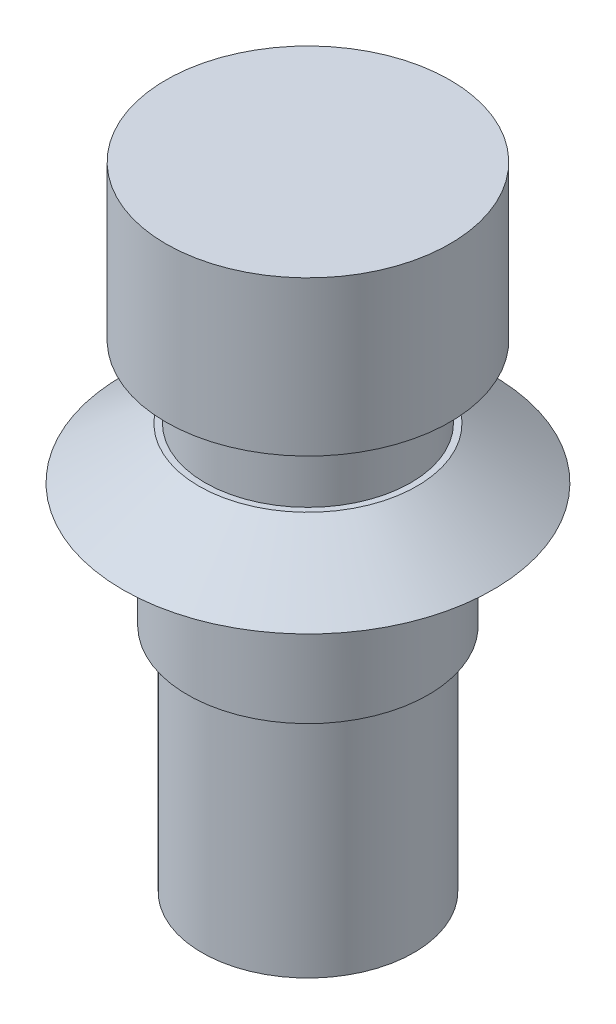
SolidWorks part; units mm, degrees
ref_plane "Спереди" through (0, 0, 0) normal (0, 0, 1) x (1, 0, 0)
ref_plane "Сверху" through (0, 0, 0) normal (0, 1, 0) x (1, 0, 0)
ref_plane "Справа" through (0, 0, 0) normal (1, 0, 0) x (0, 0, -1)
sketch "Sketch1" plane through (0, 0, 0) normal (0, 1, 0) x (1, 0, 0)
  circle A0 centre (0, 0) radius 5.85
  dimension "D1" = 11.7
extrude "Boss-Extrude1" add sketch "Sketch1" along normal blind 17.2
sketch "Sketch2" plane through (0, 17.2, 0) normal (0, 1, 0) x (1, 0, 0)
  circle A0 centre (0, 0) radius 9
  dimension "D1" = 18
extrude "Boss-Extrude2" add sketch "Sketch2" along normal blind 2.5 draft 56
sketch "Sketch3" plane through (0, 19.7, 0) normal (0, 1, 0) x (1, 0, 0)
  circle A0 centre (0, 0) radius 5
  dimension "D1" = 10
extrude "Boss-Extrude3" add sketch "Sketch3" along normal blind 3.5
sketch "Sketch4" plane through (0, 23.2, 0) normal (0, 1, 0) x (1, 0, 0)
  circle A0 centre (0, 0) radius 6.9
  dimension "D1" = 13.8
extrude "Boss-Extrude4" add sketch "Sketch4" along normal blind 7.5
sketch "Sketch5" plane through (0, 0, 0) normal (0, -1, 0) x (1, 0, 0)
  circle A0 centre (0, 0) radius 5.15
  dimension "D1" = 10.3
extrude "Cut-Extrude1" cut sketch "Sketch5" against normal blind 11.2 flip side to cut
